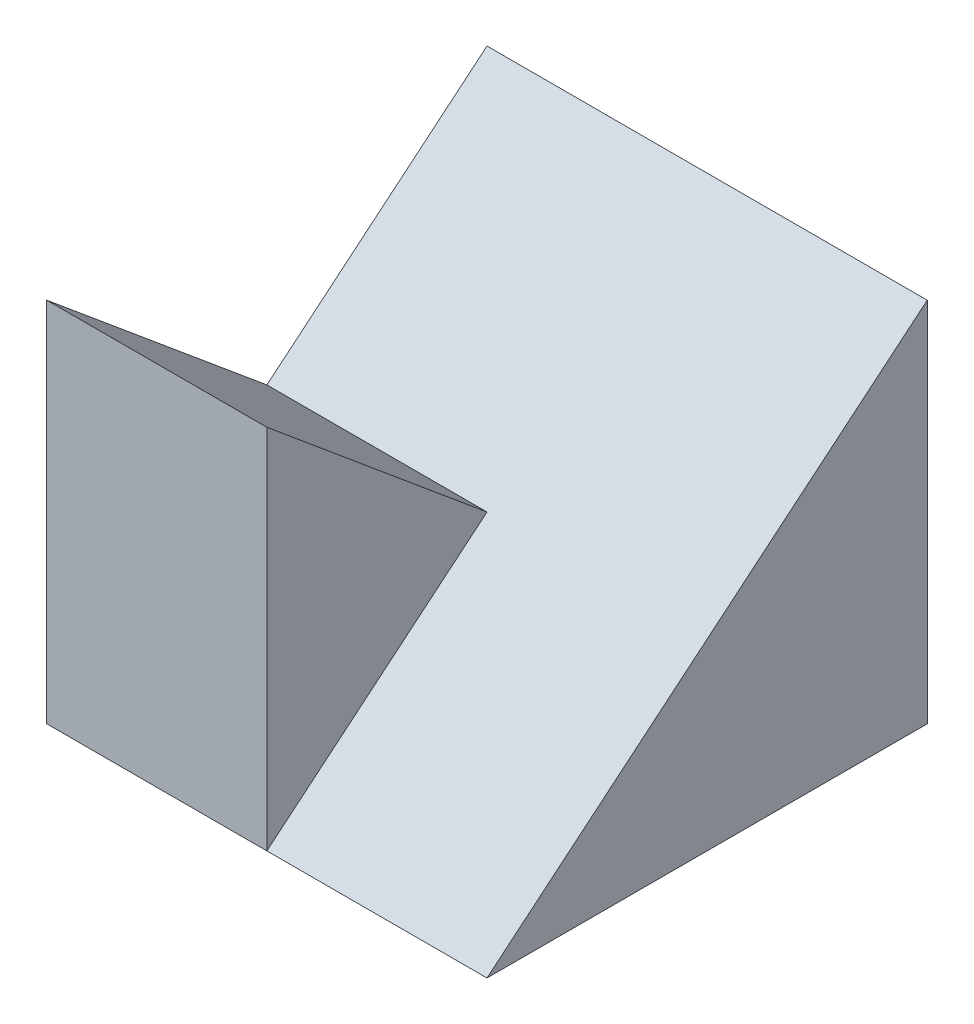
SolidWorks part; units mm, degrees
ref_plane "Front" through (0, 0, 0) normal (0, 0, 1) x (1, 0, 0)
ref_plane "Top" through (0, 0, 0) normal (0, 1, 0) x (1, 0, 0)
ref_plane "Right" through (0, 0, 0) normal (1, 0, 0) x (0, 0, -1)
sketch "Sketch1" plane through (0, 0, 0) normal (0, 1, 0) x (1, 0, 0)
  line L1 (-3, -3) -> (3, -3)
  line L2 (-3, -3) -> (-3, 3)
  line L3 (-3, 3) -> (3, 3)
  line L4 (3, -3) -> (3, 3)
  line L5 (-3, -3) -> (3, 3) construction
  line L6 (-3, 3) -> (3, -3) construction
  point P0 (0, 0)
  dimension "D1" = 6
  dimension "D2" = 6
extrude "Boss-Extrude1" add sketch "Sketch1" along normal blind 5
sketch "Sketch2" plane through (-3, 0, 0) normal (-1, 0, 0) x (0, 0, 1)
  line L0 (-3, 5) -> (0, 2.5)
  line L2 (0, 2.5) -> (3, 5)
  line L4 (-3, 0) -> (3, 0)
  line L5 (3, 0) -> (3, 5)
  line L6 (3, 5) -> (-3, 5)
  line L7 (-3, 5) -> (-3, 0)
  line L8 (-3, 0) -> (3, 0)
  line L9 (3, 0) -> (3, 5)
  line L10 (3, 5) -> (-3, 5)
  line L11 (-3, 5) -> (-3, 0)
  dimension "D1" = 0
extrude "Cut-Extrude1" cut sketch "Sketch2" against normal blind 10
sketch "Sketch3" plane through (3, 0, 0) normal (1, 0, 0) x (0, 0, -1)
  line L0 (3, 5) -> (-3, 0)
  line L6 (3, 5) -> (0, 2.5)
  line L7 (3, 5) -> (0, 2.5)
  line L8 (-3, 5) -> (-3, 0)
  line L9 (-3, 0) -> (3, 0)
  line L10 (3, 0) -> (3, 5)
  line L11 (0, 2.5) -> (-3, 5)
  line L12 (0, 2.5) -> (-3, 5)
  line L13 (-3, 5) -> (-3, 0)
  line L14 (-3, 0) -> (3, 0)
  line L15 (3, 0) -> (3, 5)
  dimension "D1" = 0
extrude "Cut-Extrude2" cut sketch "Sketch3" against normal blind 3
